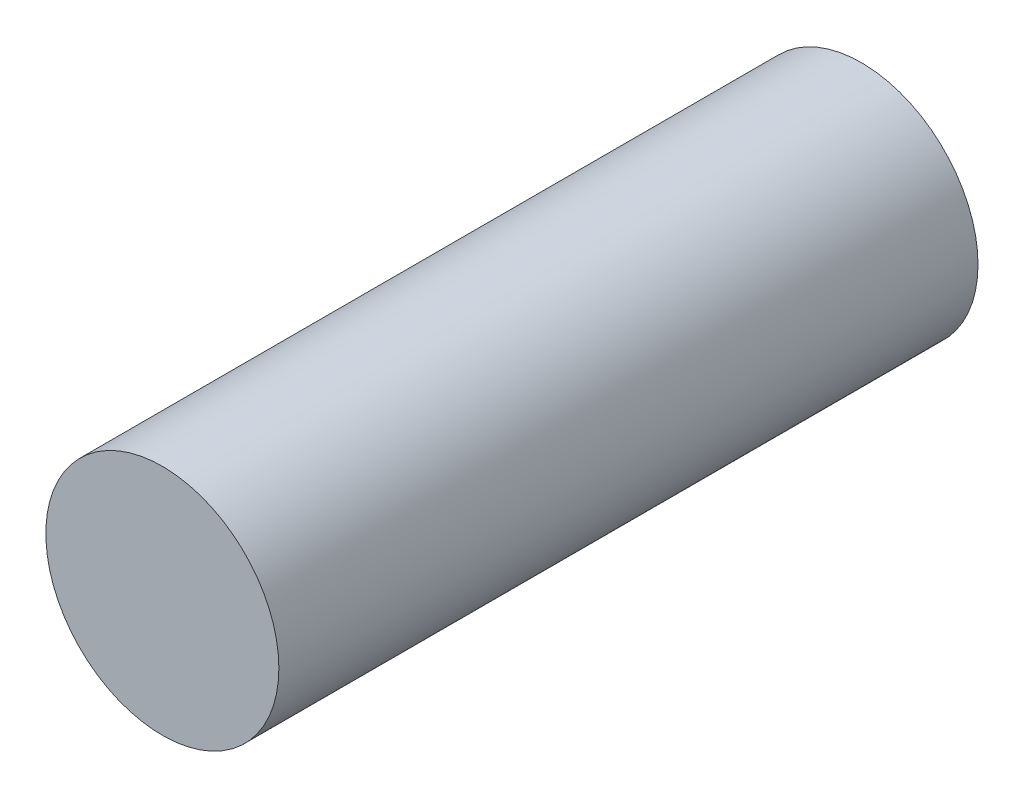
SolidWorks part; units mm, degrees
ref_plane "Plan de face" through (0, 0, 0) normal (0, 0, 1) x (1, 0, 0)
ref_plane "Plan de dessus" through (0, 0, 0) normal (0, 1, 0) x (1, 0, 0)
ref_plane "Plan de droite" through (0, 0, 0) normal (1, 0, 0) x (0, 0, -1)
sketch "Esquisse1" plane through (0, 0, 0) normal (0, 0, 1) x (1, 0, 0)
  circle A0 centre (0, 0) radius 1
extrude "Boss.-Extru.1" add sketch "Esquisse1" along normal blind 6
